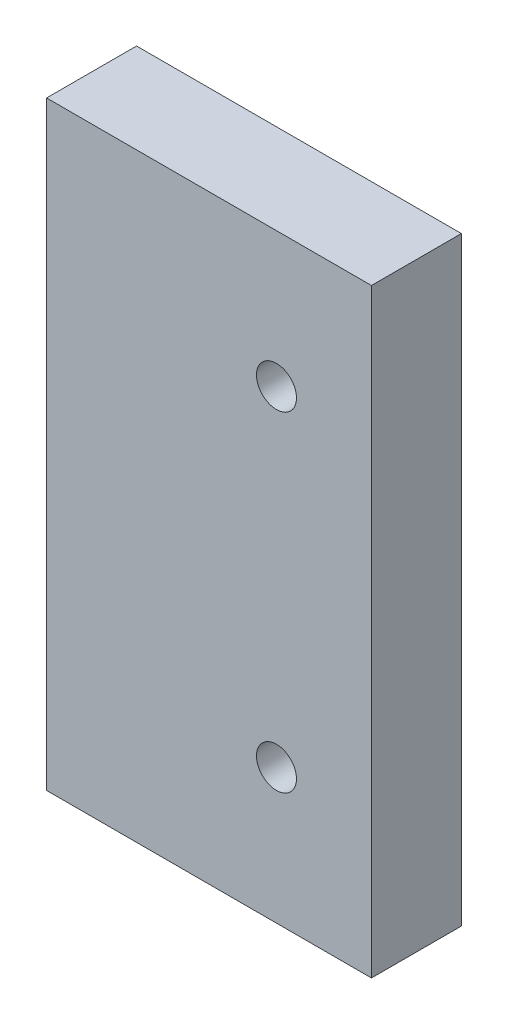
SolidWorks part; units mm, degrees
material "Balsa"
ref_plane "Front Plane" through (0, 0, 0) normal (0, 0, 1) x (1, 0, 0)
ref_plane "Top Plane" through (0, 0, 0) normal (0, 1, 0) x (1, 0, 0)
ref_plane "Right Plane" through (0, 0, 0) normal (1, 0, 0) x (0, 0, -1)
sketch "Sketch1" plane through (0, 0, 0) normal (0, 0, 1) x (1, 0, 0)
  line L1 (-32.5, 60) -> (32.5, 60)
  line L2 (-32.5, 60) -> (-32.5, -60)
  line L3 (-32.5, -60) -> (32.5, -60)
  line L4 (32.5, 60) -> (32.5, -60)
  line L5 (-32.5, 60) -> (32.5, -60) construction
  line L6 (-32.5, -60) -> (32.5, 60) construction
  circle A0 centre (13.5, 33) radius 4
  circle A1 centre (13.5, -33) radius 4
  point P0 (0, 0)
  dimension "D3" = 8
  dimension "D4" = 8
  dimension "D5" = 19
  dimension "D1" = 65
  dimension "D2" = 120
  dimension "D6" = 19
  dimension "D7" = 27
  dimension "D8" = 27
extrude "Boss-Extrude1" add sketch "Sketch1" along normal blind 18
